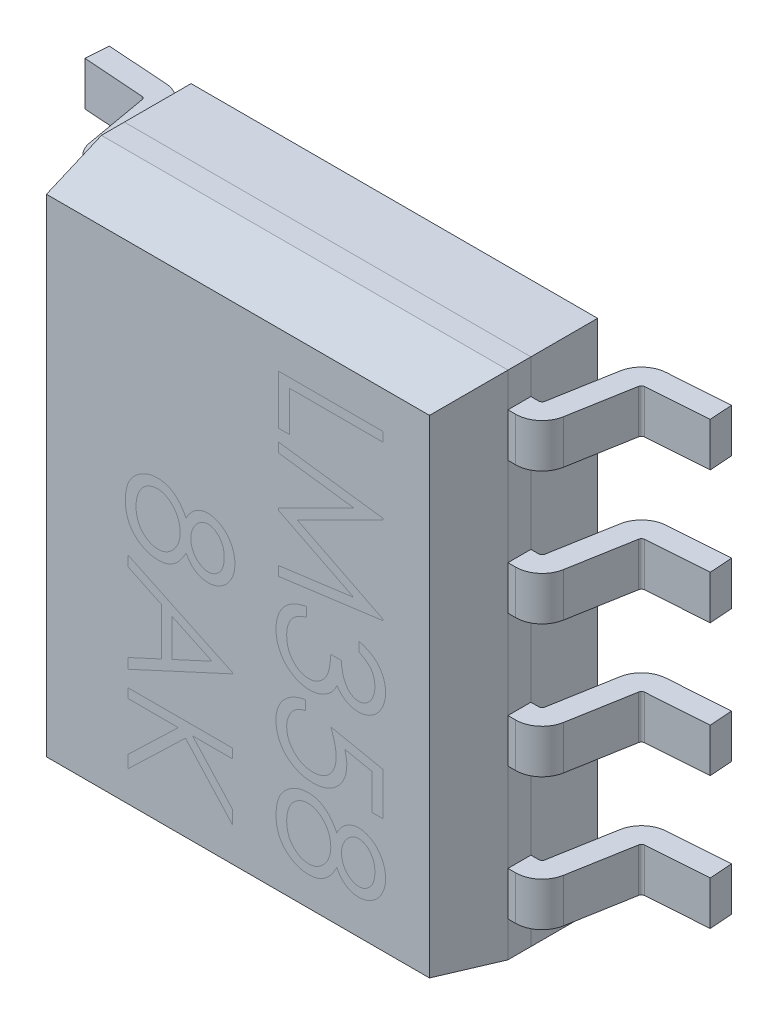
SolidWorks part; units mm, degrees
ref_plane "Front Plane" through (0, 0, 0) normal (0, 0, 1) x (1, 0, 0)
ref_plane "Top Plane" through (0, 0, 0) normal (0, 1, 0) x (1, 0, 0)
ref_plane "Right Plane" through (0, 0, 0) normal (1, 0, 0) x (0, 0, -1)
sketch "Szkic1" plane through (0, 0, 0) normal (0, 0, 1) x (1, 0, 0)
  line L1 (1.95, 2.45) -> (-1.95, 2.45)
  line L2 (1.95, 2.45) -> (1.95, -2.45)
  line L3 (1.95, -2.45) -> (-1.95, -2.45)
  line L4 (-1.95, 2.45) -> (-1.95, -2.45)
  line L5 (1.95, 2.45) -> (-1.95, -2.45) construction
  line L6 (1.95, -2.45) -> (-1.95, 2.45) construction
  point P0 (0, 0)
  dimension "D1" = 3.9
  dimension "D2" = 4.9
extrude "Dodanie-wyciągnięcie1" add sketch "Szkic1" along normal blind 0.22
ref_plane "Płaszczyzna1" through (0, -2.11, 0) normal (0, -1, 0) x (-1, 0, 0)
sketch "Szkic2" plane through (0, -2.11, 0) normal (0, -1, 0) x (-1, 0, 0)
  line L0 (1.95, 0) -> (1.95, -0.22)
  line L1 (1.95, -0.22) -> (2.024, -0.22)
  line L2 (2.2737, -0.0105) -> (2.3817, 0.6018)
  line L3 (2.4124, 0.6294) -> (3, 0.6705)
  line L4 (2.9847, 0.89) -> (2.397, 0.8489)
  line L5 (2.165, 0.64) -> (2.057, 0.0277)
  line L6 (2.024, 0) -> (1.95, 0)
  line L7 (-1.95, -0.22) -> (-1.95, 0)
  line L8 (-1.95, 0) -> (-2.024, 0)
  line L9 (-2.057, 0.0277) -> (-2.165, 0.64)
  line L10 (-2.397, 0.8489) -> (-2.9847, 0.89)
  line L11 (-2.9847, 0.89) -> (-3, 0.6705)
  line L12 (-3, 0.6705) -> (-2.4124, 0.6294)
  line L13 (-2.3817, 0.6018) -> (-2.2737, -0.0105)
  line L14 (-2.024, -0.22) -> (-1.95, -0.22)
  line L15 (1.95, -0.22) -> (-1.95, -0.22) construction
  line L16 (0, 0) -> (0, -0.22) construction
  line L17 (1.95, -0.22) -> (-1.95, -0.22) construction
  line L18 (3, 0.6705) -> (2.9847, 0.89)
  arc A0 (2.024, -0.22) -> (2.2737, -0.0105) centre (2.024, 0.0336) ccw
  arc A1 (2.4124, 0.6294) -> (2.3817, 0.6018) centre (2.4147, 0.596) ccw
  arc A2 (2.397, 0.8489) -> (2.165, 0.64) centre (2.4147, 0.596) ccw
  arc A3 (2.024, 0) -> (2.057, 0.0277) centre (2.024, 0.0336) ccw
  arc A4 (-2.057, 0.0277) -> (-2.024, 0) centre (-2.024, 0.0336) ccw
  arc A5 (-2.165, 0.64) -> (-2.397, 0.8489) centre (-2.4147, 0.596) ccw
  arc A6 (-2.3817, 0.6018) -> (-2.4124, 0.6294) centre (-2.4147, 0.596) ccw
  arc A7 (-2.2737, -0.0105) -> (-2.024, -0.22) centre (-2.024, 0.0336) ccw
  point P32 (0, -0.22)
extrude "Dodanie-wyciągnięcie2" add sketch "Szkic2" against normal blind 0.42 separate body
pattern_linear "Szyk liniowy1" count 4 spacing 1.27 along (0, 1, 0) of bodies 103 102
sketch "Szkic3" plane through (0, 0, 0.22) normal (0, 0, 1) x (1, 0, 0)
  line L4 (-1.95, 2.45) -> (-1.95, -2.45)
  line L5 (-1.95, -2.45) -> (1.95, -2.45)
  line L6 (1.95, -2.45) -> (1.95, 2.45)
  line L7 (1.95, 2.45) -> (-1.95, 2.45)
  line L8 (-1.95, 2.45) -> (-1.95, -2.45)
  line L9 (-1.95, -2.45) -> (1.95, -2.45)
  line L10 (1.95, -2.45) -> (1.95, 2.45)
  line L11 (1.95, 2.45) -> (-1.95, 2.45)
  dimension "D1" = 0
extrude "Dodanie-wyciągnięcie3" add sketch "Szkic3" along normal blind 0.64 draft 10
sketch "Szkic4" plane through (0, 0, 0) normal (0, 0, -1) x (-1, 0, 0)
  line L4 (1.95, -2.45) -> (1.95, 2.45)
  line L5 (1.95, 2.45) -> (-1.95, 2.45)
  line L6 (-1.95, 2.45) -> (-1.95, -2.45)
  line L7 (-1.95, -2.45) -> (1.95, -2.45)
  line L8 (1.95, -2.45) -> (1.95, 2.45)
  line L9 (1.95, 2.45) -> (-1.95, 2.45)
  line L10 (-1.95, 2.45) -> (-1.95, -2.45)
  line L11 (-1.95, -2.45) -> (1.95, -2.45)
  dimension "D1" = 0
extrude "Dodanie-wyciągnięcie4" add sketch "Szkic4" along normal blind 0.64 separate body
sketch "Szkic5" plane through (0, 0, 0.86) normal (0, 0, 1) x (1, 0, 0)
  line L0 (0.3903, 2.3372) -> (0.3903, -2.3372) construction
  line L1 (1.8372, 2.3372) -> (-1.8372, 2.3372) construction
  line L2 (-1.8372, -2.3372) -> (1.8372, -2.3372) construction
  line L3 (-1.0549, 2.3372) -> (-1.0549, -2.3372) construction
  text T0 "LM358" font "Century Gothic" height 1
  text T1 "    8AK" font "Century Gothic" height 1
split line "Linia podziałowa1"
